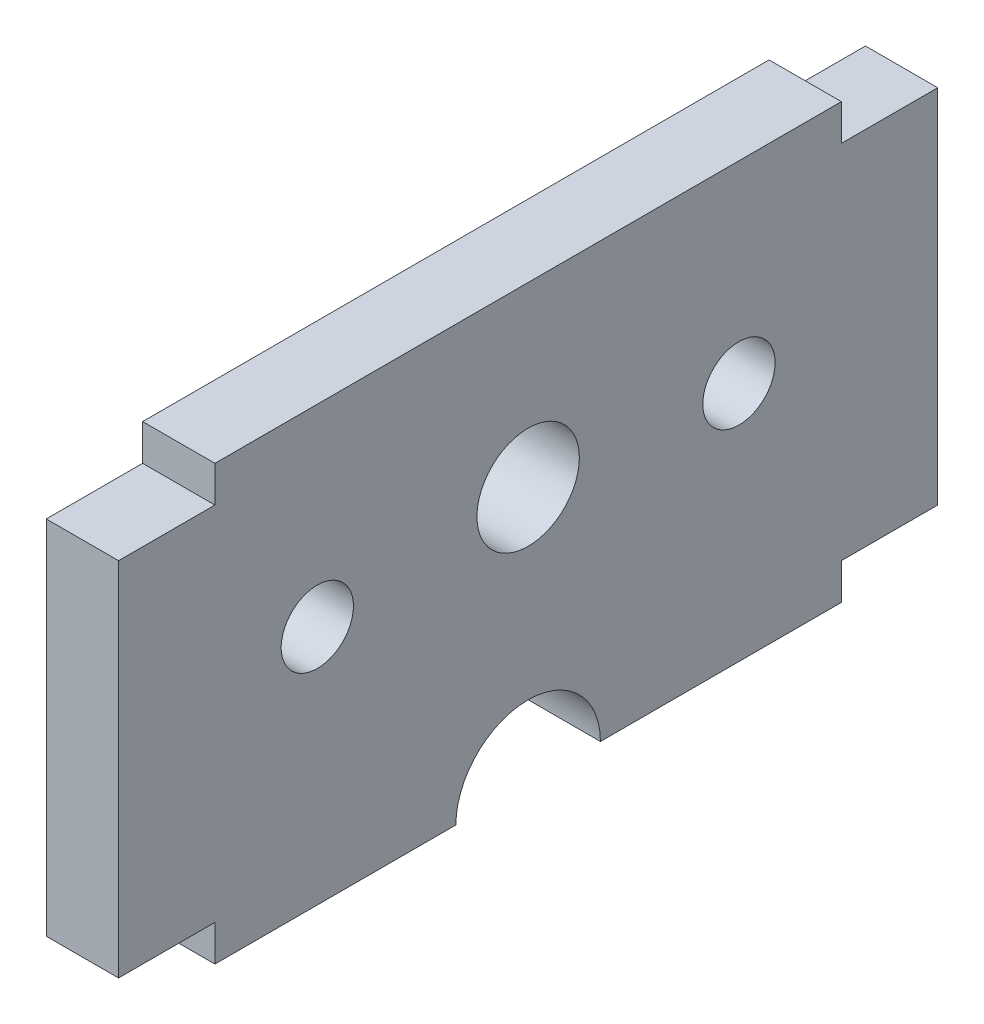
SolidWorks part; units mm, degrees
ref_plane "Front Plane" through (0, 0, 0) normal (0, 0, 1) x (1, 0, 0)
ref_plane "Top Plane" through (0, 0, 0) normal (0, 1, 0) x (1, 0, 0)
ref_plane "Right Plane" through (0, 0, 0) normal (1, 0, 0) x (0, 0, -1)
sketch "Sketch1" plane through (0, 0, 0) normal (1, 0, 0) x (0, 0, -1)
  line L1 (13, 6.5) -> (17, 6.5)
  line L2 (-13, -10) -> (13, -10)
  line L3 (-13, -10) -> (-13, -8.5)
  line L4 (-13, 8) -> (13, 8)
  line L5 (13, -10) -> (13, -8.5)
  line L6 (17, 6.5) -> (17, -8.5)
  line L7 (17, -8.5) -> (13, -8.5)
  line L8 (0, 0) -> (0, 13.945) construction
  line L9 (-17, -8.5) -> (-13, -8.5)
  line L10 (-17, 6.5) -> (-17, -8.5)
  line L11 (-13, 6.5) -> (-17, 6.5)
  line L12 (13, 6.5) -> (13, 8)
  line L13 (-13, 6.5) -> (-13, 8)
  circle A0 centre (-8.75, 0) radius 1.5
  circle A1 centre (8.75, 0) radius 1.5
  dimension "D3" = 3
  dimension "D4" = 3
  dimension "D5" = 10
  dimension "D6" = 8
  dimension "D8" = 13
  dimension "D9" = 18
  dimension "D10" = 4
  dimension "D11" = 15
  dimension "D12" = 1.5
extrude "Boss-Extrude1" add sketch "Sketch1" along normal blind 3
sketch "Sketch2" plane through (3, 0, 0) normal (1, 0, 0) x (0, 0, -1)
  line L0 (-13, -10) -> (13, -10) construction
  line L1 (-3, -10) -> (3, -10)
  arc A0 (3, -10) -> (-3, -10) centre (0, -10) ccw
  dimension "D1" = 3
extrude "Cut-Extrude1" cut sketch "Sketch2" against normal blind 3
sketch "Sketch3" plane through (3, 0, 0) normal (1, 0, 0) x (0, 0, -1)
  circle A2 centre (0, 0.6411) radius 2.125
  dimension "D1" = 4.25
extrude "Cut-Extrude3" cut sketch "Sketch3" against normal through all
